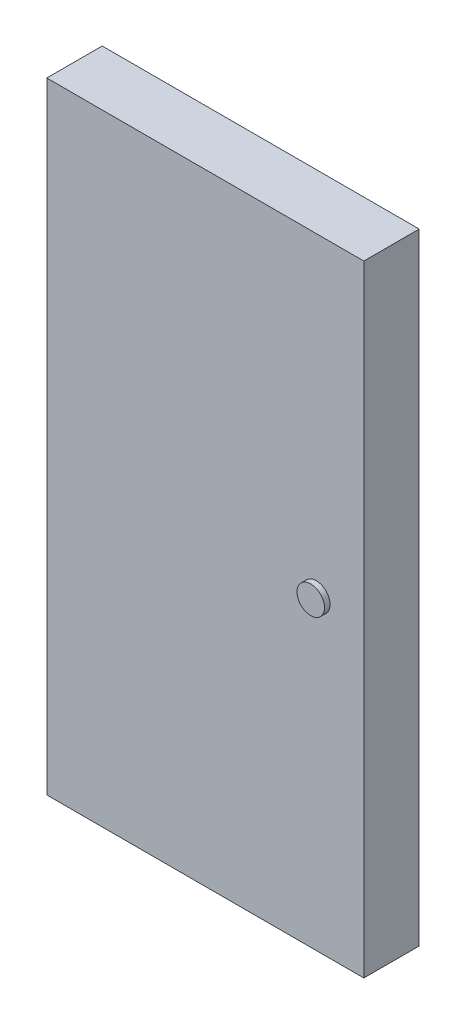
SolidWorks part; units mm, degrees
ref_plane "Alzado" through (0, 0, 0) normal (0, 0, 1) x (1, 0, 0)
ref_plane "Planta" through (0, 0, 0) normal (0, 1, 0) x (1, 0, 0)
ref_plane "Vista lateral" through (0, 0, 0) normal (1, 0, 0) x (0, 0, -1)
sketch "Croquis1" plane through (0, 0, 0) normal (0, 0, 1) x (1, 0, 0)
  line L1 (-1459.6554, 1702.6473) -> (257.3946, 1702.6473)
  line L2 (-1459.6554, 1702.6473) -> (-1459.6554, -1660.1827)
  line L3 (-1459.6554, -1660.1827) -> (257.3946, -1660.1827)
  line L4 (257.3946, 1702.6473) -> (257.3946, -1660.1827)
  dimension "D1" = 3362.83
  dimension "D2" = 1717.05
extrude "Saliente-Extruir1" add sketch "Croquis1" along normal blind 300
sketch "Croquis2" plane through (0, 0, 300) normal (0, 0, 1) x (1, 0, 0)
  circle A0 centre (0, 0) radius 74.4613
extrude "Saliente-Extruir2" add sketch "Croquis2" along normal blind 30
